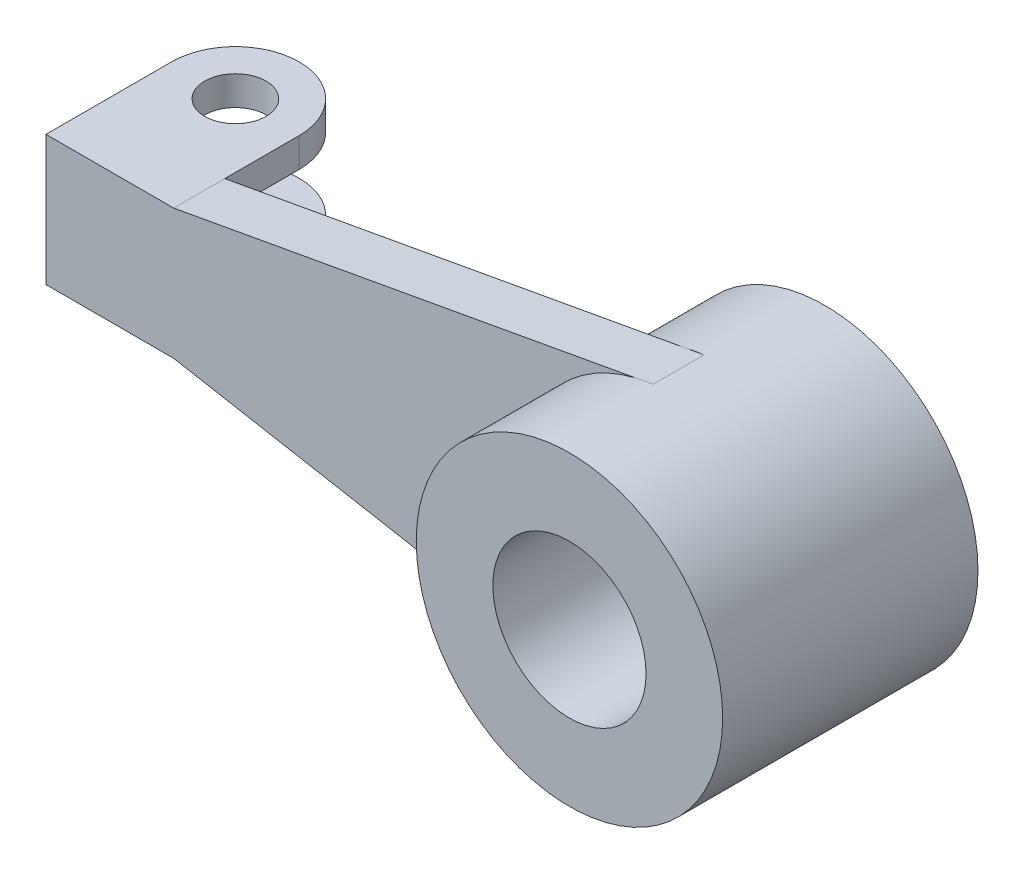
SolidWorks part; units mm, degrees
ref_plane "Front Plane" through (0, 0, 0) normal (0, 0, 1) x (1, 0, 0)
ref_plane "Top Plane" through (0, 0, 0) normal (0, 1, 0) x (1, 0, 0)
ref_plane "Right Plane" through (0, 0, 0) normal (1, 0, 0) x (0, 0, -1)
sketch "Sketch1" plane through (0, 0, 0) normal (0, 0, 1) x (1, 0, 0)
  line L0 (0, 0) -> (1154.7945, 0) construction
  line L1 (-70.2055, 127.3973) -> (-70.2055, -127.3973)
  line L2 (-70.2055, -127.3973) -> (179.7945, -127.3973)
  line L3 (179.7945, -127.3973) -> (1118.4184, -297.7865)
  line L4 (-70.2055, 127.3973) -> (179.7945, 127.3973)
  line L5 (179.7945, 127.3973) -> (1118.4184, 297.7865)
  arc A0 (1084.1839, -291.5719) -> (1084.1839, 291.5719) centre (1154.7945, 0) ccw
  circle A1 centre (1154.7945, 0) radius 150
  dimension "D1" = 300
  dimension "D2" = 600
  dimension "D3" = 1225
  dimension "D4" = 250
extrude "Boss-Extrude3" add sketch "Sketch1" along normal mid plane 50
sketch "Sketch6" plane through (0, 0, 25) normal (0, 0, 1) x (1, 0, 0)
  circle A0 centre (1154.7945, 0) radius 150
  circle A1 centre (1154.7945, 0) radius 300
extrude "Boss-Extrude6" add sketch "Sketch6" along normal blind 200
mirror "Mirror1" about plane through (0, 0, -25) normal (0, 0, 1) of "Boss-Extrude6", "Boss-Extrude3"
sketch "Sketch9" plane through (0, 127.3973, 0) normal (0, 1, 0) x (1, 0, 0)
  line L0 (-70.2055, 75) -> (179.7945, 75)
  line L1 (-70.2055, 75) -> (-70.2055, 220.8644)
  line L2 (179.7945, 75) -> (179.7945, 220.8644)
  line L3 (-5.2055, 220.8644) -> (114.7945, 220.8644)
  arc A0 (179.7945, 220.8644) -> (-70.2055, 220.8644) centre (54.7945, 220.8644) ccw
  circle A1 centre (54.7945, 220.8644) radius 60
  line M3 (179.7945, 75) -> (-70.2055, 75)
  dimension "D1" = 145.8644
extrude "Boss-Extrude8" add sketch "Sketch9" against normal blind 254.1897 contours L2 A0 L1 A1 M3
sketch "Sketch10" plane through (-70.2055, 0, 0) normal (-1, 0, 0) x (0, 0, 1)
  line L0 (0, 0) -> (-302.9119, 0) construction
  line L1 (-75, -70) -> (-75, 70)
  line L2 (-75, 0) -> (-375, 0)
  line L3 (-375, 70) -> (-375, -70)
  line L4 (-375, -70) -> (-75, -70)
  line L5 (-375, 70) -> (-75, 70)
  line M7 (-220.8644, 127.3973) -> (-220.8644, -126.7924)
  dimension "D1" = 300
  dimension "D2" = 70
extrude "Cut-Extrude1" cut sketch "Sketch10" against normal blind 300 contours L4 L1 L2 M7 | L3 L4 L2 M7 | L5 L3 L2 M7 | L5 L2 L1 M7
